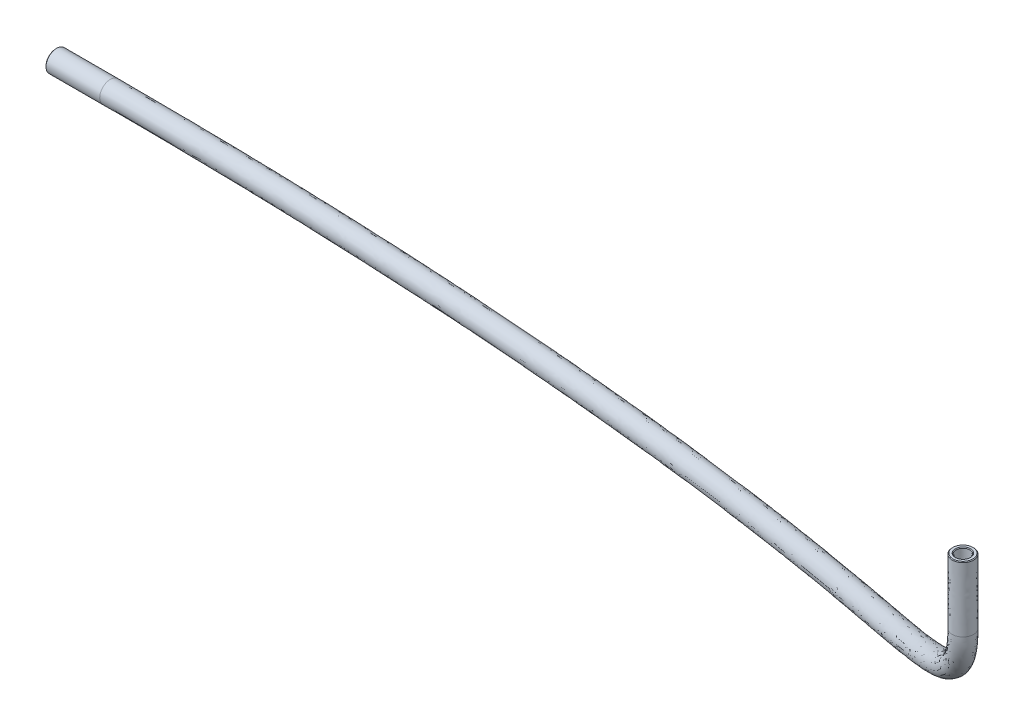
SolidWorks part; units mm, degrees
ref_plane "Front Plane" through (0, 0, 0) normal (0, 0, 1) x (1, 0, 0)
ref_plane "Top Plane" through (0, 0, 0) normal (0, 1, 0) x (1, 0, 0)
ref_plane "Right Plane" through (0, 0, 0) normal (1, 0, 0) x (0, 0, -1)
sketch3d "3DSketch1"
  line L0 (-136.8853, -106.4823, -25.525) -> (-147.0853, -106.4823, -25.525)
  line L1 (62.325, -62.125, 13.85) -> (62.325, -74.325, 13.85)
  spline S0 degree 3 poles (62.325, -74.325, 13.85) (62.325, -85.1225, 13.85) (31.4608, -98.363, -5.8375) (-64.5259, -106.4823, -25.525) (-136.8853, -106.4823, -25.525) knots 0 0 0 0 0.441562 1 1 1 1
sketch "Sketch1" plane through (-139.3853, 0, 0) normal (1, 0, 0) x (0, 0, -1)
  circle A0 centre (25.525, -106.4823) radius 1.3
  circle A1 centre (25.525, -106.4823) radius 2
  circle A2 centre (25.525, -106.4823) radius 3.8416 construction
  dimension "D1" = 2.6
  dimension "D2" = 4
sweep "Sweep1" add profiles "Sketch1" path "3DSketch1"
chamfer "Chamfer1" distance 0.127 angle 45 4 edges at (-147.0853, -104.4823, -25.525) (-147.0853, -105.1823, -25.525) (61.2297, -62.125, 12.1766) (61.6131, -62.125, 12.7623)
